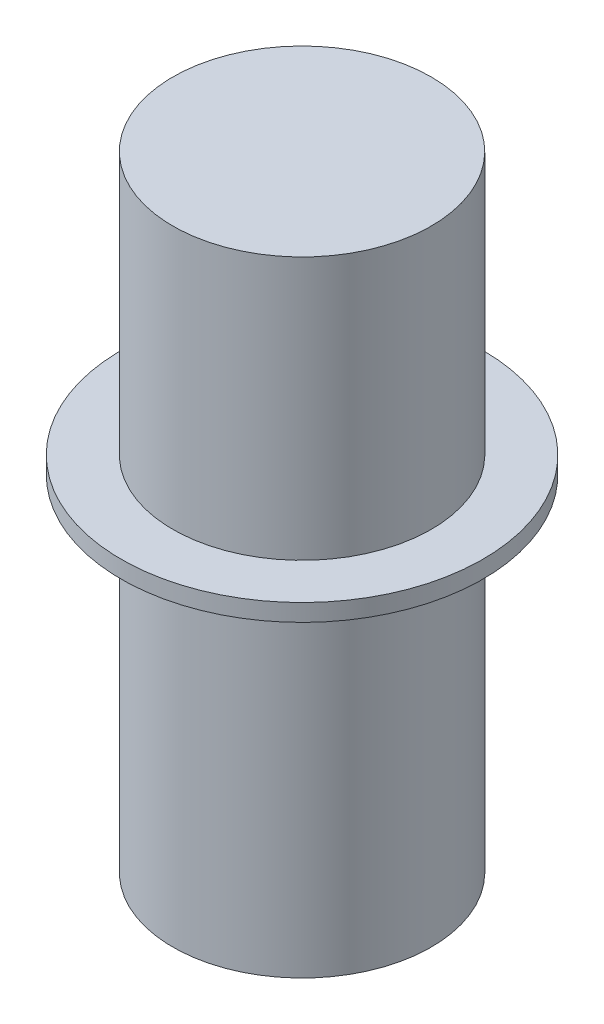
SolidWorks part; units mm, degrees
ref_plane "Plano frontal" through (0, 0, 0) normal (0, 0, 1) x (1, 0, 0)
ref_plane "Plano superior" through (0, 0, 0) normal (0, 1, 0) x (1, 0, 0)
ref_plane "Plano direito" through (0, 0, 0) normal (1, 0, 0) x (0, 0, -1)
sketch "Esboço1" plane through (0, 0, 0) normal (0, 0, 1) x (1, 0, 0)
  line L0 (0, -22.4951) -> (0, 84.2569) construction
  line L1 (0, 0) -> (-15, 0)
  line L2 (-15, 0) -> (-15, 40)
  line L3 (-15, 40) -> (-21, 40)
  line L6 (-21, 40) -> (-21, 42)
  line L7 (-21, 42) -> (-15, 42)
  line L8 (-15, 42) -> (-15, 72.5)
  line L9 (-15, 72.5) -> (0, 72.5)
  line L10 (0, 0) -> (0, 72.5)
  dimension "D1" = 15
  dimension "D2" = 15
  dimension "D3" = 30.5
  dimension "D4" = 42
  dimension "D5" = 21
revolve "Revolução1" add sketch "Esboço1" angle 360 about L0
